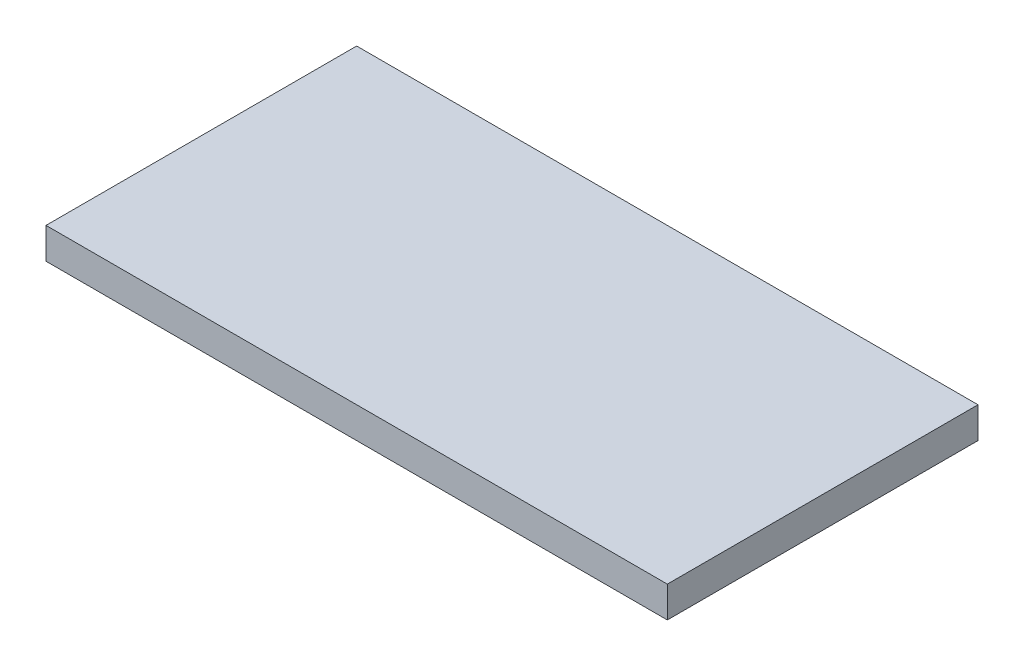
SolidWorks part; units mm, degrees
ref_plane "Front" through (0, 0, 0) normal (0, 0, 1) x (1, 0, 0)
ref_plane "Top" through (0, 0, 0) normal (0, 1, 0) x (1, 0, 0)
ref_plane "Right" through (0, 0, 0) normal (1, 0, 0) x (0, 0, -1)
sketch "草图1" plane through (0, 0, 0) normal (0, 1, 0) x (1, 0, 0)
  line L1 (-500, -250) -> (500, -250)
  line L2 (-500, -250) -> (-500, 250)
  line L3 (-500, 250) -> (500, 250)
  line L4 (500, -250) -> (500, 250)
  line L5 (-500, -250) -> (500, 250) construction
  line L6 (-500, 250) -> (500, -250) construction
  point P0 (0, 0)
  dimension "D1" = 1000
  dimension "D2" = 500
extrude "凸台-拉伸1" add sketch "草图1" along normal blind 50
